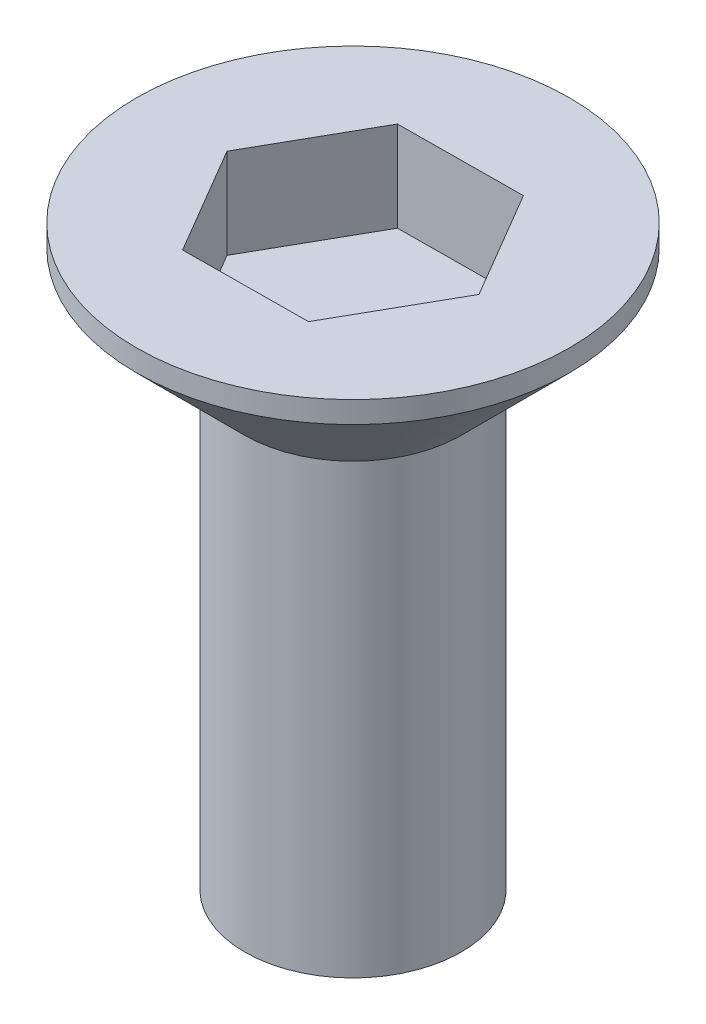
SolidWorks part; units mm, degrees
ref_plane "Спереди" through (0, 0, 0) normal (0, 0, 1) x (1, 0, 0)
ref_plane "Сверху" through (0, 0, 0) normal (0, 1, 0) x (1, 0, 0)
ref_plane "Справа" through (0, 0, 0) normal (1, 0, 0) x (0, 0, -1)
sketch "Эскиз1" plane through (0, 0, 0) normal (0, 0, 1) x (1, 0, 0)
  line L0 (0, 0) -> (3, 0)
  line L1 (3, 0) -> (3, 12.4)
  line L2 (3, 12.4) -> (6, 15.4)
  line L3 (6, 15.4) -> (6, 16)
  line L4 (6, 16) -> (0, 16)
  line L5 (0, 68.6446) -> (0, -29.1082) construction
  line L6 (0, 0) -> (0, 16)
  point P9 (0, 0)
revolve "Повернуть1" add sketch "Эскиз1" angle 360 about L5
sketch "Эскиз2" plane through (0, 16, 0) normal (0, 1, 0) x (1, 0, 0)
  line L1 (1.7553, -2.9865) -> (3.464, 0.0269)
  line L2 (3.464, 0.0269) -> (1.7087, 3.0133)
  line L3 (1.7087, 3.0133) -> (-1.7553, 2.9865)
  line L4 (-1.7553, 2.9865) -> (-3.464, -0.0269)
  line L5 (-3.464, -0.0269) -> (-1.7087, -3.0133)
  line L6 (-1.7087, -3.0133) -> (1.7553, -2.9865)
  circle A0 centre (0, 0) radius 3 construction
extrude "Вырез-Вытянуть1" cut sketch "Эскиз2" against normal blind 2.5
